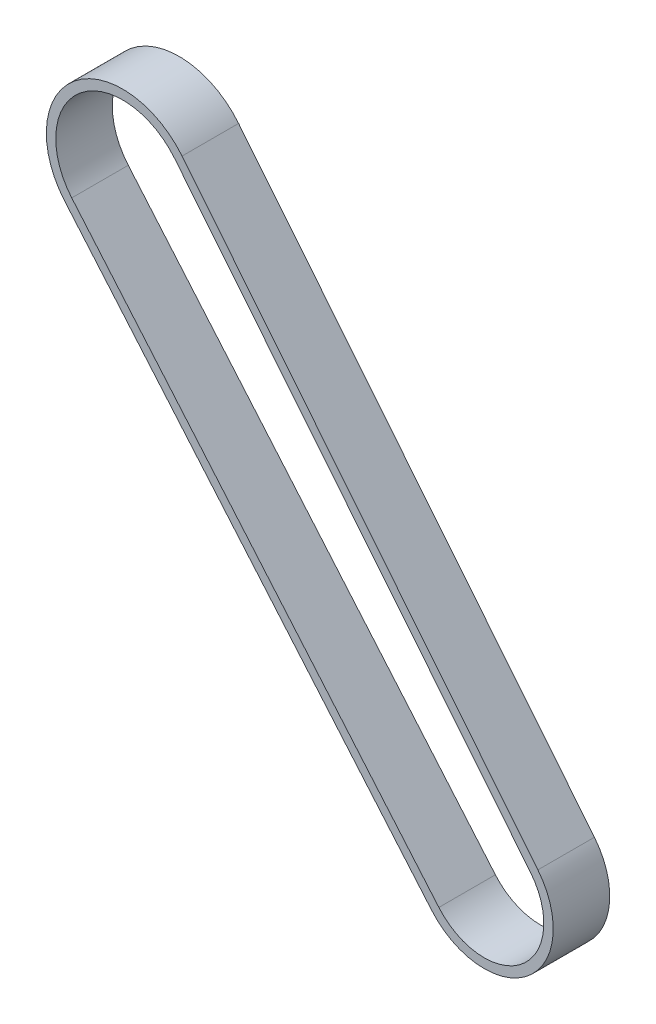
SolidWorks part; units mm, degrees
ref_plane "前视基准面" through (0, 0, 0) normal (0, 0, 1) x (1, 0, 0)
ref_plane "上视基准面" through (0, 0, 0) normal (0, 1, 0) x (1, 0, 0)
ref_plane "右视基准面" through (0, 0, 0) normal (1, 0, 0) x (0, 0, -1)
sketch "草图2" plane through (0, 0, 0) normal (0, 0, 1) x (1, 0, 0)
  line L0 (0, 0) -> (1, 0) construction
  line L1 (0, 0) -> (0, 1) construction
  line L2 (5.5252, 4.4654) -> (43.2933, -42.2661)
  line L3 (33.5595, -50.3438) -> (-5.4075, -4.6072)
  arc A0 (-5.4075, -4.6072) -> (5.5252, 4.4654) centre (0, 0) cw
  arc A1 (43.2933, -42.2661) -> (33.5595, -50.3438) centre (38.3741, -46.2419) cw
extrude "拉伸-薄壁1" add sketch "草图2" along normal blind 6 thin thin type one direction wall 1
